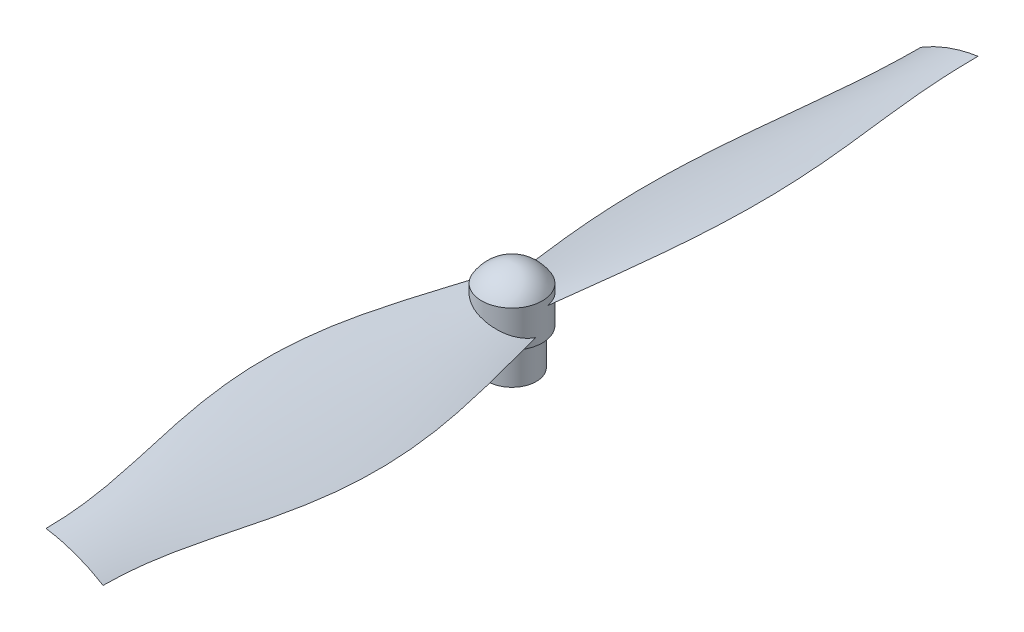
SolidWorks part; units mm, degrees
ref_plane "Front Plane" through (0, 0, 0) normal (0, 0, 1) x (1, 0, 0)
ref_plane "Top Plane" through (0, 0, 0) normal (0, 1, 0) x (1, 0, 0)
ref_plane "Right Plane" through (0, 0, 0) normal (1, 0, 0) x (0, 0, -1)
sketch "Sketch1" plane through (0, 0, 0) normal (0, 0, 1) x (1, 0, 0)
  line L0 (0, 0) -> (0, 15)
  line L1 (0, 0) -> (4, 0)
  line L2 (4, 0) -> (4, 6)
  line L3 (4, 6) -> (5, 6)
  line L4 (5, 6) -> (5, 12)
  arc A0 (0, 15) -> (5, 12) centre (-0.198, 9.0033) cw
  dimension "D6" = 6
  dimension "D1" = 15
  dimension "D2" = 4
  dimension "D3" = 6
  dimension "D4" = 1
  dimension "D5" = 6
revolve "Revolve1" add sketch "Sketch1" angle 360 about L0
sketch "Sketch2" plane through (0, 0, 0) normal (0, -1, 0) x (1, 0, 0)
  line L1 (1.4434, -2.5) -> (2.8868, 0)
  line L2 (2.8868, 0) -> (1.4434, 2.5)
  line L3 (1.4434, 2.5) -> (-1.4434, 2.5)
  line L4 (-1.4434, 2.5) -> (-2.8868, 0)
  line L5 (-2.8868, 0) -> (-1.4434, -2.5)
  line L6 (-1.4434, -2.5) -> (1.4434, -2.5)
  circle A0 centre (0, 0) radius 2.5 construction
  dimension "D1" = 5
extrude "Cut-Extrude1" cut sketch "Sketch2" against normal blind 7
ref_plane "Plane1" through (0, 0, 20) normal (0, 0, 1) x (1, 0, 0)
ref_plane "Plane3" through (0, 0, 72) normal (0, 0, 1) x (1, 0, 0)
sketch "Sketch3" plane through (0, 0, 0) normal (0, 0, 1) x (1, 0, 0)
  line L0 (0, 0) -> (0, 15) construction
  line L1 (4.6985, 7.2899) -> (-4.6985, 10.7101) construction
  line L2 (-4, 0) -> (4, 0) construction
  arc A0 (-4.6985, 10.7101) -> (4.6985, 7.2899) centre (-8.3777, -14.0177) cw
  point P7 (0, 9)
  dimension "D4" = 25
  dimension "D1" = 10
  dimension "D2" = 70
  dimension "D3" = 9
sketch "Sketch4" plane through (0, 0, 20) normal (0, 0, 1) x (1, 0, 0)
  line L0 (0, 0) -> (0, 15) construction
  line L1 (-8.4572, 12.0782) -> (8.4572, 5.9218) construction
  line L3 (-4, 0) -> (4, 0) construction
  arc A0 (-8.4572, 12.0782) -> (8.4572, 5.9218) centre (-27.1879, -65.6982) cw
  point P8 (0, 9)
  dimension "D4" = 80
  dimension "D1" = 18
  dimension "D2" = 70
  dimension "D3" = 9
sketch "Sketch5" plane through (0, 0, 72) normal (0, 0, 1) x (1, 0, 0)
  line L0 (0, 0) -> (0, 15) construction
  line L1 (-4.6985, 10.7101) -> (4.6985, 7.2899) construction
  line L2 (-4, 0) -> (4, 0) construction
  arc A0 (-4.6985, 10.7101) -> (4.6985, 7.2899) centre (-8.3777, -14.0177) cw
  point P8 (0, 9)
  dimension "D4" = 25
  dimension "D1" = 10
  dimension "D2" = 70
  dimension "D3" = 9
surface "Surface-Loft1"
ref_plane "Plane4" through (0, 0, -20) normal (0, 0, 1) x (1, 0, 0)
ref_plane "Plane5" through (0, 0, -72) normal (0, 0, 1) x (1, 0, 0)
sketch "Sketch7" plane through (0, 0, 0) normal (0, 0, 1) x (1, 0, 0)
  line L0 (0, 0) -> (0, 15) construction
  line L1 (4.6985, 10.7101) -> (-4.6985, 7.2899) construction
  line L2 (-4, 0) -> (4, 0) construction
  arc A0 (4.6985, 10.7101) -> (-4.6985, 7.2899) centre (8.3777, -14.0177) ccw
  point P7 (0, 9)
  dimension "D4" = 25
  dimension "D1" = 10
  dimension "D2" = 70
  dimension "D3" = 9
sketch "Sketch8" plane through (0, 0, -20) normal (0, 0, 1) x (1, 0, 0)
  line L0 (0, 0) -> (0, 15) construction
  line L1 (8.4572, 12.0782) -> (-8.4572, 5.9218) construction
  line L3 (-4, 0) -> (4, 0) construction
  arc A0 (8.4572, 12.0782) -> (-8.4572, 5.9218) centre (27.1879, -65.6982) ccw
  point P8 (0, 9)
  dimension "D4" = 80
  dimension "D1" = 18
  dimension "D2" = 70
  dimension "D3" = 9
sketch "Sketch9" plane through (0, 0, -72) normal (0, 0, 1) x (1, 0, 0)
  line L0 (0, 0) -> (0, 15) construction
  line L1 (4.6985, 10.7101) -> (-4.6985, 7.2899) construction
  line L2 (-4, 0) -> (4, 0) construction
  arc A0 (4.6985, 10.7101) -> (-4.6985, 7.2899) centre (8.3777, -14.0177) ccw
  point P8 (0, 9)
  dimension "D4" = 25
  dimension "D1" = 10
  dimension "D2" = 70
  dimension "D3" = 9
surface "Surface-Loft2"
